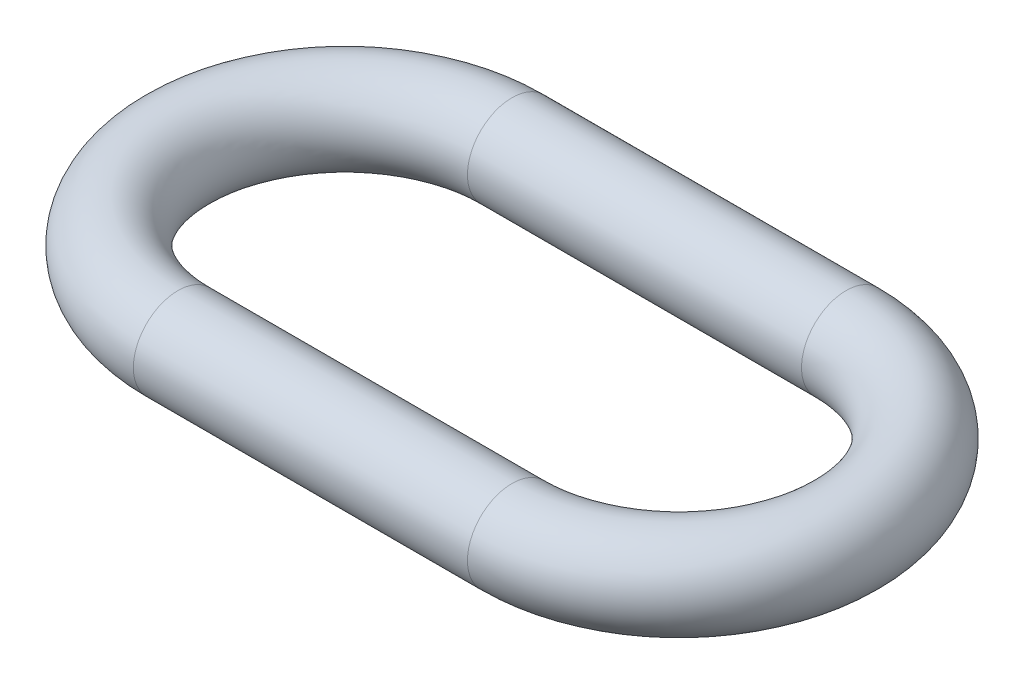
SolidWorks part; units mm, degrees
ref_plane "Front Plane" through (0, 0, 0) normal (0, 0, 1) x (1, 0, 0)
ref_plane "Top Plane" through (0, 0, 0) normal (0, 1, 0) x (1, 0, 0)
ref_plane "Right Plane" through (0, 0, 0) normal (1, 0, 0) x (0, 0, -1)
sketch "Sketch1" plane through (0, 0, 0) normal (0, 1, 0) x (1, 0, 0)
  line L0 (-28.6102, 0) -> (-43.6102, 0) construction
  line L1 (-28.6102, -7.5) -> (-43.6102, -7.5)
  line L2 (-28.6102, 7.5) -> (-43.6102, 7.5)
  arc A0 (-28.6102, -7.5) -> (-28.6102, 7.5) centre (-28.6102, 0) ccw
  arc A1 (-43.6102, 7.5) -> (-43.6102, -7.5) centre (-43.6102, 0) ccw
  point P3 (-36.1102, 0)
  dimension "D1" = 15
  dimension "D2" = 15
sketch "Sketch5" plane through (0, 0, 0) normal (0, 0, 1) x (1, 0, 0)
  line L0 (-21.1102, 0) -> (-28.6102, 0) construction
  line L1 (-43.6102, 0) -> (-51.1102, 0) construction
  line L3 (-51.1102, 2) -> (-51.1102, -2)
  line L4 (-21.1102, 2) -> (-21.1102, -2)
  circle A0 centre (-21.1102, 0) radius 2
  circle A1 centre (-51.1102, 0) radius 2
  point P12 (-49.1102, 0)
  point P13 (-23.1102, 0)
  dimension "D1" = 4
sweep "Sweep4" add profiles "Sketch5" path "Sketch1"
